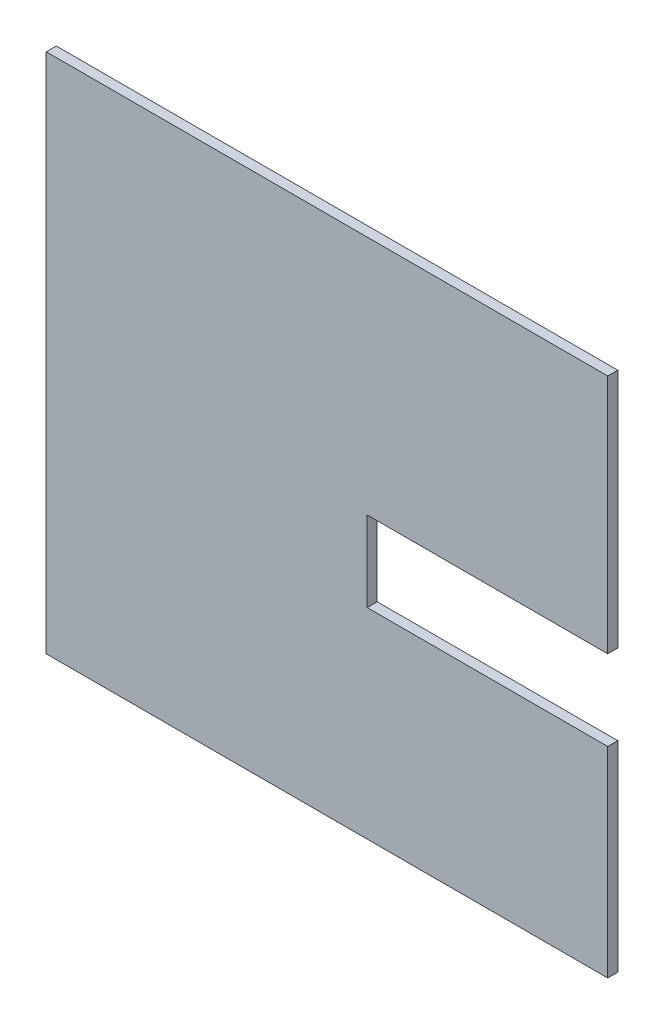
SolidWorks part; units mm, degrees
material "ALUMINUM 6061-T6"
ref_plane "Front Plane" through (0, 0, 0) normal (0, 0, 1) x (1, 0, 0)
ref_plane "Top Plane" through (0, 0, 0) normal (0, 1, 0) x (1, 0, 0)
ref_plane "Right Plane" through (0, 0, 0) normal (1, 0, 0) x (0, 0, -1)
sketch "Sketch1" plane through (0, 0, 0) normal (0, 0, 1) x (1, 0, 0)
  line L1 (-177.8, -165.1) -> (177.8, -165.1)
  line L2 (-177.8, -165.1) -> (-177.8, 165.1)
  line L3 (-177.8, 165.1) -> (177.8, 165.1)
  line L4 (177.8, -165.1) -> (177.8, 165.1)
  line L5 (-177.8, -165.1) -> (177.8, 165.1) construction
  line L6 (-177.8, 165.1) -> (177.8, -165.1) construction
  point P0 (0, 0)
  dimension "D1" = 355.6
  dimension "D2" = 330.2
extrude "Boss-Extrude1" add sketch "Sketch1" along normal mid plane 6.35
sketch "Sketch3" plane through (0, 0, 3.175) normal (0, 0, 1) x (1, 0, 0)
  line L0 (177.8, -165.1) -> (177.8, 165.1) construction
  line L1 (177.8, -38.1) -> (25.4, -38.1)
  line L2 (177.8, -38.1) -> (177.8, 12.7)
  line L3 (177.8, 12.7) -> (25.4, 12.7)
  line L4 (25.4, -38.1) -> (25.4, 12.7)
  line L5 (-177.8, -165.1) -> (177.8, -165.1) construction
  dimension "D1" = 152.4
  dimension "D2" = 50.8
  dimension "D3" = 127
extrude "Cut-Extrude1" cut sketch "Sketch3" against normal through all
